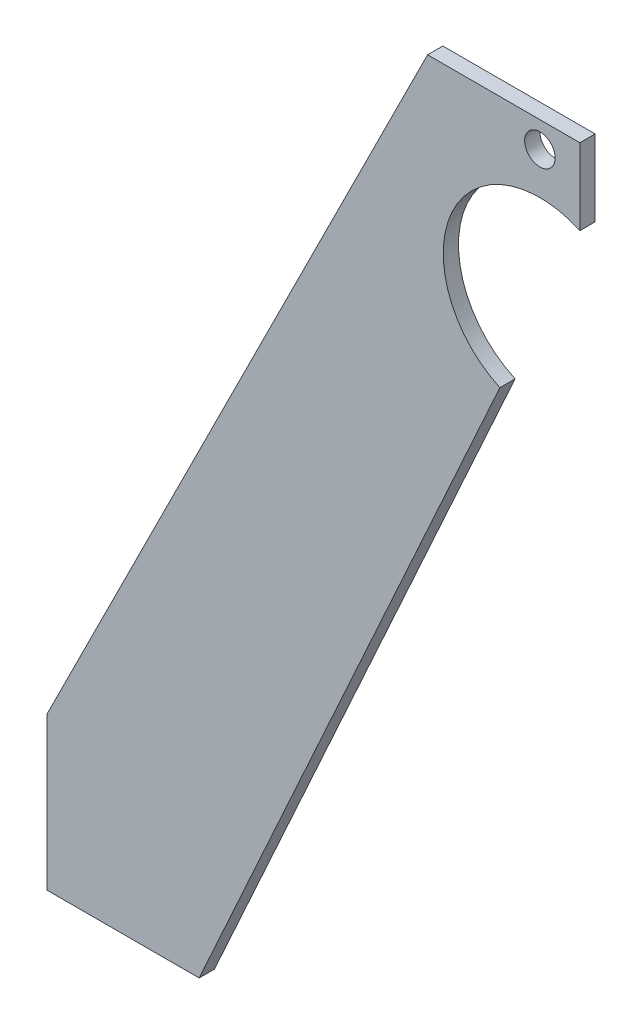
SolidWorks part; units mm, degrees
ref_plane "Front Plane" through (0, 0, 0) normal (0, 0, 1) x (1, 0, 0)
ref_plane "Top Plane" through (0, 0, 0) normal (0, 1, 0) x (1, 0, 0)
ref_plane "Right Plane" through (0, 0, 0) normal (1, 0, 0) x (0, 0, -1)
sketch "Sketch1" plane through (0, 0, 0) normal (0, 0, 1) x (1, 0, 0)
  line L0 (0, 0) -> (0, -40)
  line L1 (0, -40) -> (40, -40)
  line L2 (0, 0) -> (0, 200) construction
  line L3 (40, -40) -> (140, -40) construction
  line L4 (140, 200) -> (100, 200)
  line L5 (140, 200) -> (140, 180)
  line L6 (118.9915, 133.7813) -> (40, -40)
  line L7 (100, 200) -> (0, 0)
  arc A0 (140, 180) -> (118.9915, 133.7813) centre (129.4957, 156.8906) ccw
  circle A1 centre (129.4957, 193.2312) radius 4
  dimension "D2" = 40
  dimension "D1" = 40
extrude "Boss-Extrude1" add sketch "Sketch1" along normal blind 4
